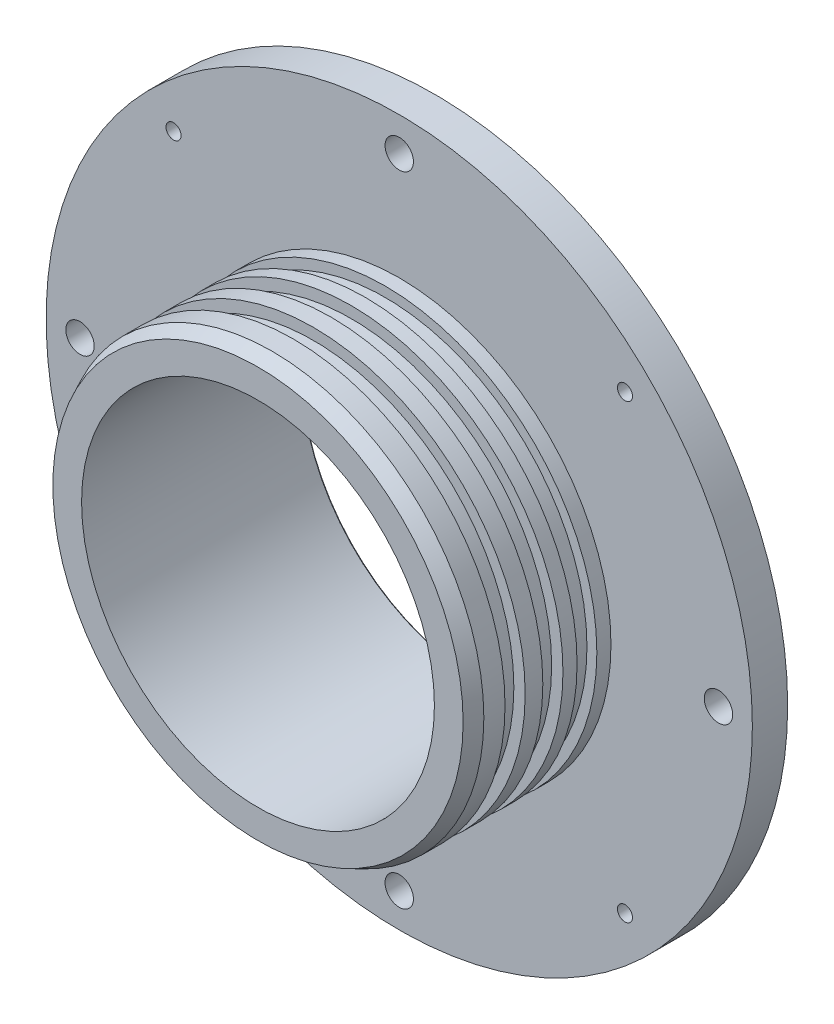
SolidWorks part; units mm, degrees
material "6061-T6 (SS)"
ref_plane "Front Plane" through (0, 0, 0) normal (0, 0, 1) x (1, 0, 0)
ref_plane "Top Plane" through (0, 0, 0) normal (0, 1, 0) x (1, 0, 0)
ref_plane "Right Plane" through (0, 0, 0) normal (1, 0, 0) x (0, 0, -1)
sketch "Sketch1" plane through (0, 0, 0) normal (0, 1, 0) x (1, 0, 0)
  line L0 (63.5, 0) -> (45.9994, 0)
  line L1 (63.5, 0) -> (63.5, -6.35)
  line L2 (63.5, -6.35) -> (38.0746, -6.35)
  line L3 (38.0746, -6.35) -> (38.0746, -8.89)
  line L4 (38.0746, -31.75) -> (31.7246, -31.75)
  line L5 (31.7246, -6.35) -> (31.7246, -31.75)
  line L6 (38.0746, -14.986) -> (36.0426, -14.986)
  line L7 (36.0426, -14.986) -> (36.0426, -18.6055)
  line L8 (36.0426, -18.6055) -> (38.0746, -18.6055)
  line L9 (38.0746, -18.6055) -> (38.0746, -21.7805)
  line L10 (38.0746, -21.7805) -> (36.0426, -21.7805)
  line L11 (36.0426, -21.7805) -> (36.0426, -25.4)
  line L12 (36.0426, -25.4) -> (38.0746, -25.4)
  line L13 (38.0746, -25.4) -> (38.0746, -31.75)
  line L14 (31.7246, -6.35) -> (0, -6.35)
  line L15 (0, -6.35) -> (0, 0)
  line L16 (45.9994, 0) -> (45.9994, 0.254)
  line L17 (45.9994, 0.254) -> (43.2181, 0.254)
  line L18 (43.2181, 0.254) -> (43.2181, 5.0292)
  line L19 (43.2181, 5.0292) -> (45.9994, 5.0292)
  line L20 (45.9994, 5.0292) -> (45.9994, 8.2)
  line L21 (30.7594, 8.2) -> (45.9994, 8.2)
  line L22 (30.7594, 8.2) -> (30.7594, 0)
  line L23 (30.7594, 0) -> (0, 0)
  line L24 (38.0746, -8.89) -> (36.2966, -8.89)
  line L25 (36.2966, -8.89) -> (36.2966, -12.446)
  line L26 (36.2966, -12.446) -> (38.0746, -12.446)
  line L27 (38.0746, -12.446) -> (38.0746, -14.986)
  dimension "D1" = 25.4
  dimension "D2" = 6.35
  dimension "D3" = 6.35
  dimension "D4" = 38.0746
  dimension "D5" = 3.6195
  dimension "D6" = 3.175
  dimension "D7" = 6.35
  dimension "D8" = 36.0426
  dimension "D9" = 63.5
  dimension "D10" = 6.35
  dimension "D11" = 45.9994
  dimension "D12" = 8.2
  dimension "D13" = 15.24
  dimension "D14" = 43.2181
  dimension "D15" = 4.7752
  dimension "D16" = 0.254
  dimension "D17" = 3.556
  dimension "D18" = 1.778
  dimension "D19" = 2.54
revolve "Revolve1" add sketch "Sketch1" angle 360 about L15
chamfer "Chamfer2" distance 1.27 angle 45 2 edges at (45.9994, 0, -8.2) (30.7594, 0, -8.2)
sketch "Sketch7" plane through (0, 0, 6.35) normal (0, 0, 1) x (1, 0, 0)
  circle A0 centre (0, 0) radius 31.7246
  circle A1 centre (0, 0) radius 31.7246 construction
extrude "Cut-Extrude1" cut sketch "Sketch7" against normal through all
hole_wizard "#6-32 Tapped Hole1" positions "Sketch11" profile "Sketch10" tap size "#6-32" standard "ANSI Inch" end condition through all
sketch "Sketch11" plane through (0, 0, 0) normal (0, 0, -1) x (-1, 0, 0)
  line L0 (0, 0) -> (50000, 0) construction
  line L1 (0, 0) -> (35355.3391, 35355.3391) construction
  point P7 (40.5908, 40.5908)
  dimension "D1" = 45
  dimension "D2" = 57.404
sketch "Sketch10" plane through (-40.5908, 40.5908, 0) normal (1, 0, 0) x (0, 1, 0)
  line L0 (0, 0) -> (0, 31.75)
  line L1 (0, 31.75) -> (1.3525, 31.75)
  line L2 (1.3525, 31.75) -> (1.3525, 0)
  line L5 (1.3525, 0) -> (0, 0)
  line L11 (0, -6.35) -> (0, 107.95) construction
  dimension "Thread Major Dia." = 2.7051
  dimension "Thru Tap Drill Depth" = 31.75
pattern_circular "CirPattern2" count 4 over 360 about axis through (0, 0, 0) along (0, 0, 1) of "#6-32 Tapped Hole1"
hole_wizard "#10 Clearance Hole1" positions "Sketch13" profile "Sketch14" hole size "#10" standard "ANSI Inch" end condition through all
sketch "Sketch13" plane through (0, 0, 0) normal (0, 0, -1) x (-1, 0, 0)
  line L0 (0, 0) -> (0, 50000) construction
  point P0 (0, 57.404)
  dimension "D1" = 57.404
sketch "Sketch14" plane through (0, 57.404, 0) normal (1, 0, 0) x (0, 1, 0)
  line L0 (0, 0) -> (0, 31.75)
  line L1 (0, 31.75) -> (2.5527, 31.75)
  line L2 (2.5527, 31.75) -> (2.5527, 0)
  line L5 (2.5527, 0) -> (0, 0)
  line L11 (0, -6.35) -> (0, 107.95) construction
  dimension "Thru Hole Dia." = 5.1054
  dimension "Thru Hole Depth" = 31.75
pattern_circular "CirPattern3" count 4 over 360 about axis through (0, 0, 0) along (0, 0, 1) of "#10 Clearance Hole1"
chamfer "Chamfer1" distance 2.54 angle 25 1 edges at (38.0746, 0, 31.75)
sketch "Sketch15" [suppressed] plane through (0, 0, 6.35) normal (0, 0, 1) x (1, 0, 0)
  line L0 (0, 0) -> (0, 9.8107) construction
  line L1 (0, 0) -> (54.3796, 54.3796) construction
  line L4 (26.7998, 35.7801) -> (31.29, 40.2702)
  line L5 (31.29, 40.2702) -> (40.2702, 31.29)
  line L6 (35.7801, 26.7998) -> (40.2702, 31.29)
  line L7 (26.7998, 35.7801) -> (40.2702, 31.29) construction
  line L8 (31.29, 40.2702) -> (35.7801, 26.7998) construction
  arc A0 (26.7998, 35.7801) -> (35.7801, 26.7998) centre (0, 0) cw
  point P4 (33.535, 33.535)
  dimension "D4" = 44.704
  dimension "D1" = 6.35
  dimension "D2" = 12.7
  dimension "D3" = 45
extrude "Boss-Extrude1" [suppressed] add sketch "Sketch15" along normal blind 7.62
hole_wizard "#6-32 Tapped Hole3" [suppressed] positions "Sketch17" profile "Sketch16" tap size "#6-32" standard "ANSI Inch"
sketch "Sketch17" [suppressed] plane through (35.7801, 35.7801, 0) normal (0.7071, 0.7071, 0) x (0, 0, -1)
  line L0 (0, 0) -> (-50000, 0) construction
  line L1 (-10.16, 0) -> (-10.16, -50000) construction
  line L4 (-13.97, -6.35) -> (-13.97, 6.35) construction
  point P0 (-10.16, 0)
  dimension "D1" = 3.81
sketch "Sketch16" [suppressed] plane through (35.7801, 35.7801, 10.16) normal (0, 0, 1) x (-0.7071, 0.7071, 0)
  line L0 (0, 0) -> (0, 18.8761)
  line L1 (0, 18.8761) -> (1.3525, 18.8761)
  line L2 (1.3525, 18.8761) -> (1.3525, 0)
  line L5 (1.3525, 0) -> (0, 0)
  line L11 (0, -6.35) -> (0, 107.95) construction
  dimension "Thread Major Dia." = 2.7051
  dimension "Thru Tap Drill Depth" = 18.8761
chamfer "Chamfer3" [suppressed] distance 0.762 angle 45
fillet "Fillet2" [suppressed] radius 1.27
pattern_circular "CirPattern4" [suppressed] count 4 over 360
ref_plane "Plane1" through (2.54, 0, 0) normal (1, 0, 0) x (0, 0, -1)
